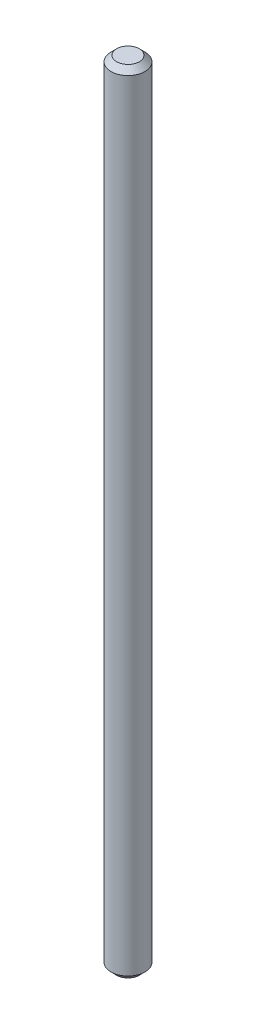
SolidWorks part; units mm, degrees
ref_plane "Front Plane" through (0, 0, 0) normal (0, 0, 1) x (1, 0, 0)
ref_plane "Top Plane" through (0, 0, 0) normal (0, 1, 0) x (1, 0, 0)
ref_plane "Right Plane" through (0, 0, 0) normal (1, 0, 0) x (0, 0, -1)
sketch "Sketch2" plane through (0, 0, 0) normal (0, 1, 0) x (1, 0, 0)
  circle A0 centre (0, 0) radius 1.5
  dimension "D1" = 3
extrude "Boss-Extrude1" add sketch "Sketch2" along normal blind 70
chamfer "Chamfer1" distance 0.5 angle 45 2 edges at (0, 0, 1.5) (0, 70, 1.5)
